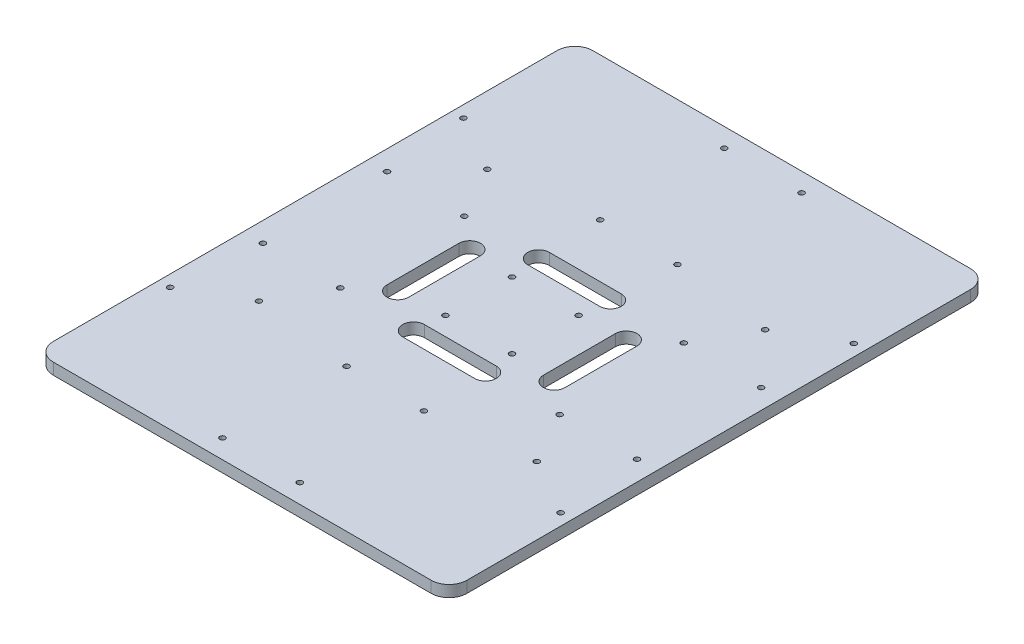
SolidWorks part; units mm, degrees
ref_plane "Front" through (0, 0, 0) normal (0, 0, 1) x (1, 0, 0)
ref_plane "Top" through (0, 0, 0) normal (0, 1, 0) x (1, 0, 0)
ref_plane "Right" through (0, 0, 0) normal (1, 0, 0) x (0, 0, -1)
sketch "草图1" plane through (0, 0, 0) normal (0, 1, 0) x (1, 0, 0)
  line L0 (-64.5848, 56.6788) -> (-64.5848, -223.3212)
  line L1 (-54.5848, -233.3212) -> (155.4152, -233.3212)
  line L2 (165.4152, -223.3212) -> (165.4152, 56.6788)
  line L3 (155.4152, 66.6788) -> (-54.5848, 66.6788)
  arc A0 (165.4152, -223.3212) -> (155.4152, -233.3212) centre (155.4152, -223.3212) cw
  arc A1 (-54.5848, -233.3212) -> (-64.5848, -223.3212) centre (-54.5848, -223.3212) cw
  arc A2 (165.4152, 56.6788) -> (155.4152, 66.6788) centre (155.4152, 56.6788) ccw
  arc A3 (-64.5848, 56.6788) -> (-54.5848, 66.6788) centre (-54.5848, 56.6788) cw
  point P6 (165.4152, -233.3212)
  point P9 (-64.5848, -233.3212)
  point P14 (-64.5848, 66.6788)
  dimension "D3" = 10
  dimension "D1" = 300
  dimension "D2" = 230
extrude "凸台-拉伸1" add sketch "草图1" along normal blind 6.35
sketch "草图2" plane through (0, 6.35, 0) normal (0, 1, 0) x (1, 0, 0)
  line L0 (-64.5848, -83.3212) -> (165.4152, -83.3212) construction
  line L1 (-64.5848, 56.6788) -> (-64.5848, -223.3212) construction
  line L2 (50.4152, 66.6788) -> (50.4152, -233.3212) construction
  line L4 (165.4152, -223.3212) -> (165.4152, 56.6788) construction
  line L6 (30.4152, -118.0712) -> (70.4152, -118.0712) construction
  line L7 (30.4152, -124.0712) -> (70.4152, -124.0712)
  line L8 (30.4152, -48.5712) -> (70.4152, -48.5712) construction
  line L9 (30.4152, -112.0712) -> (70.4152, -112.0712)
  line L10 (30.4152, -42.5712) -> (70.4152, -42.5712)
  line L11 (30.4152, -54.5712) -> (70.4152, -54.5712)
  line L12 (155.4152, 66.6788) -> (-54.5848, 66.6788) construction
  line L13 (-54.5848, -233.3212) -> (155.4152, -233.3212) construction
  line L14 (6.9152, -63.3212) -> (6.9152, -103.3212) construction
  line L15 (93.9152, -63.3212) -> (93.9152, -103.3212) construction
  line L16 (12.9152, -63.3212) -> (12.9152, -103.3212)
  line L17 (0.9152, -63.3212) -> (0.9152, -103.3212)
  line L18 (87.9152, -63.3212) -> (87.9152, -103.3212)
  line L19 (99.9152, -63.3212) -> (99.9152, -103.3212)
  circle A0 centre (68.9152, -64.8212) radius 1.5
  circle A1 centre (68.9152, -101.8212) radius 1.5
  circle A2 centre (31.9152, -101.8212) radius 1.5
  circle A3 centre (31.9152, -64.8212) radius 1.5
  circle A4 centre (111.4152, -48.8212) radius 1.5
  circle A5 centre (154.4152, -48.8212) radius 1.5
  circle A6 centre (111.4152, -117.8212) radius 1.5
  circle A7 centre (154.4152, -117.8212) radius 1.5
  circle A8 centre (-53.5848, -117.8212) radius 1.5
  circle A9 centre (-10.5848, -117.8212) radius 1.5
  circle A10 centre (-53.5848, -48.8212) radius 1.5
  circle A11 centre (-10.5848, -48.8212) radius 1.5
  circle A12 centre (28.9152, -222.8212) radius 1.5
  circle A13 centre (28.9152, -153.8212) radius 1.5
  circle A14 centre (71.9152, -222.8212) radius 1.5
  circle A15 centre (71.9152, -153.8212) radius 1.5
  circle A16 centre (71.9152, 56.1788) radius 1.5
  circle A17 centre (28.9152, 56.1788) radius 1.5
  circle A18 centre (71.9152, -12.8212) radius 1.5
  circle A19 centre (28.9152, -12.8212) radius 1.5
  arc A20 (30.4152, -42.5712) -> (30.4152, -54.5712) centre (30.4152, -48.5712) ccw
  arc A21 (70.4152, -54.5712) -> (70.4152, -42.5712) centre (70.4152, -48.5712) ccw
  arc A22 (30.4152, -124.0712) -> (30.4152, -112.0712) centre (30.4152, -118.0712) cw
  arc A23 (70.4152, -112.0712) -> (70.4152, -124.0712) centre (70.4152, -118.0712) cw
  arc A24 (12.9152, -63.3212) -> (0.9152, -63.3212) centre (6.9152, -63.3212) ccw
  arc A25 (0.9152, -103.3212) -> (12.9152, -103.3212) centre (6.9152, -103.3212) ccw
  arc A26 (87.9152, -63.3212) -> (99.9152, -63.3212) centre (93.9152, -63.3212) cw
  arc A27 (99.9152, -103.3212) -> (87.9152, -103.3212) centre (93.9152, -103.3212) cw
  circle A28 centre (127.6652, -146.7912) radius 1.5
  circle A29 centre (158.9452, -164.8512) radius 1.5
  circle A30 centre (158.9452, -1.7912) radius 1.5
  circle A31 centre (127.6652, -19.8512) radius 1.5
  circle A32 centre (-58.1148, -1.7912) radius 1.5
  circle A33 centre (-26.8348, -19.8512) radius 1.5
  circle A34 centre (-58.1148, -164.8512) radius 1.5
  circle A35 centre (-26.8348, -146.7912) radius 1.5
  point P55 (50.4152, -118.0712)
  point P58 (50.4152, -48.5712)
  point P73 (6.9152, -83.3212)
  point P78 (93.9152, -83.3212)
  dimension "D3" = 3
  dimension "D6" = 70.5
  dimension "D8" = 3
  dimension "D11" = 3
  dimension "D12" = 3
  dimension "D14" = 6
  dimension "D17" = 6
  dimension "D20" = 3
  dimension "D23" = 3
  dimension "D2" = 18.5
  dimension "D4" = 31.28
  dimension "D5" = 34.5
  dimension "D7" = 43
  dimension "D9" = 16.25
  dimension "D10" = 69
  dimension "D13" = 40
  dimension "D15" = 18.06
  dimension "D16" = 20
extrude "切除-拉伸1" cut sketch "草图2" against normal through all contours A8 | A9 | A25 L16 A24 L17 | A10 | A11 | L11 A21 L10 A20 | L7 A23 L9 A22 | A27 L18 A26 L19 | A13 | A15 | A12 | A14 | A7 | A6 | A4 | A5 | A17 | A19 | A18 | A16 | A2 | A1 | A0 | A3 | A31 | A30 | A32 | A33 | A34 | A35 | A29 | A28
